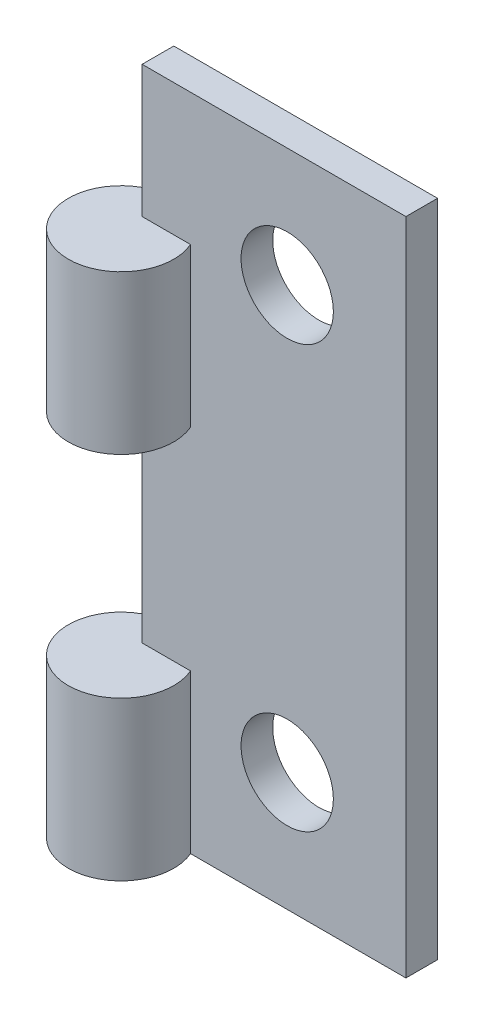
SolidWorks part; units mm, degrees
material "1060 合金"
ref_plane "前视基准面" through (0, 0, 0) normal (0, 0, 1) x (1, 0, 0)
ref_plane "上视基准面" through (0, 0, 0) normal (0, 1, 0) x (1, 0, 0)
ref_plane "右视基准面" through (0, 0, 0) normal (1, 0, 0) x (0, 0, -1)
sketch "草图1" plane through (0, 0, 0) normal (0, 0, 1) x (1, 0, 0)
  line L1 (-5, -12.5) -> (5, -12.5)
  line L2 (-5, -12.5) -> (-5, 12.5)
  line L3 (-5, 12.5) -> (5, 12.5)
  line L4 (5, -12.5) -> (5, 12.5)
  line L5 (0, 12.5) -> (0, -12.5) construction
  line L6 (-5, 0) -> (5, 0) construction
  circle A0 centre (0.5, 8) radius 1.75
  circle A1 centre (0.5, -8) radius 1.75
  point P0 (0, 0)
  dimension "D5" = 3.5
  dimension "D1" = 10
  dimension "D2" = 25
  dimension "D3" = 16
  dimension "D4" = 5.5
extrude "凸台-拉伸1" add sketch "草图1" along normal blind 1.2
sketch "草图3" plane through (0, -12.5, 0) normal (0, -1, 0) x (1, 0, 0)
  line L0 (-5, 1.2) -> (-5, 0) construction
  circle A0 centre (-5, 2) radius 2
  dimension "D1" = 4
extrude "凸台-拉伸3" add sketch "草图3" against normal blind 6
pattern_linear "阵列(线性)2" count 2 spacing 14 along (0, 1, 0) of "凸台-拉伸3"
